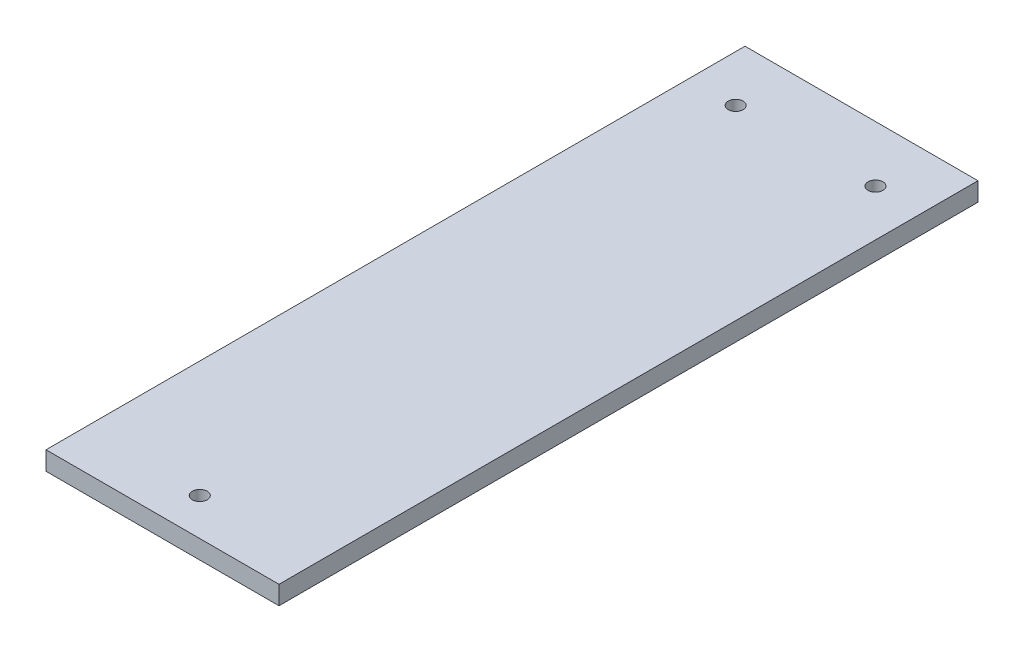
SolidWorks part; units mm, degrees
ref_plane "前视基准面" through (0, 0, 0) normal (0, 0, 1) x (1, 0, 0)
ref_plane "上视基准面" through (0, 0, 0) normal (0, 1, 0) x (1, 0, 0)
ref_plane "右视基准面" through (0, 0, 0) normal (1, 0, 0) x (0, 0, -1)
sketch "草图1" plane through (0, 0, 0) normal (0, 1, 0) x (1, 0, 0)
  line L0 (0, 75) -> (0, -75) construction
  line L1 (25, -75) -> (-25, -75)
  line L2 (25, -75) -> (25, 75)
  line L3 (25, 75) -> (-25, 75)
  line L4 (-25, -75) -> (-25, 75)
  line L5 (25, -75) -> (-25, 75) construction
  line L6 (25, 75) -> (-25, -75) construction
  circle A0 centre (-15, 63) radius 1.6
  circle A1 centre (15, 63) radius 1.6
  circle A2 centre (0, -67) radius 1.6
  point P0 (0, 0)
  dimension "D3" = 10
  dimension "D5" = 8
  dimension "D1" = 150
  dimension "D2" = 50
  dimension "D4" = 12
extrude "凸台-拉伸1" add sketch "草图1" along normal blind 4
